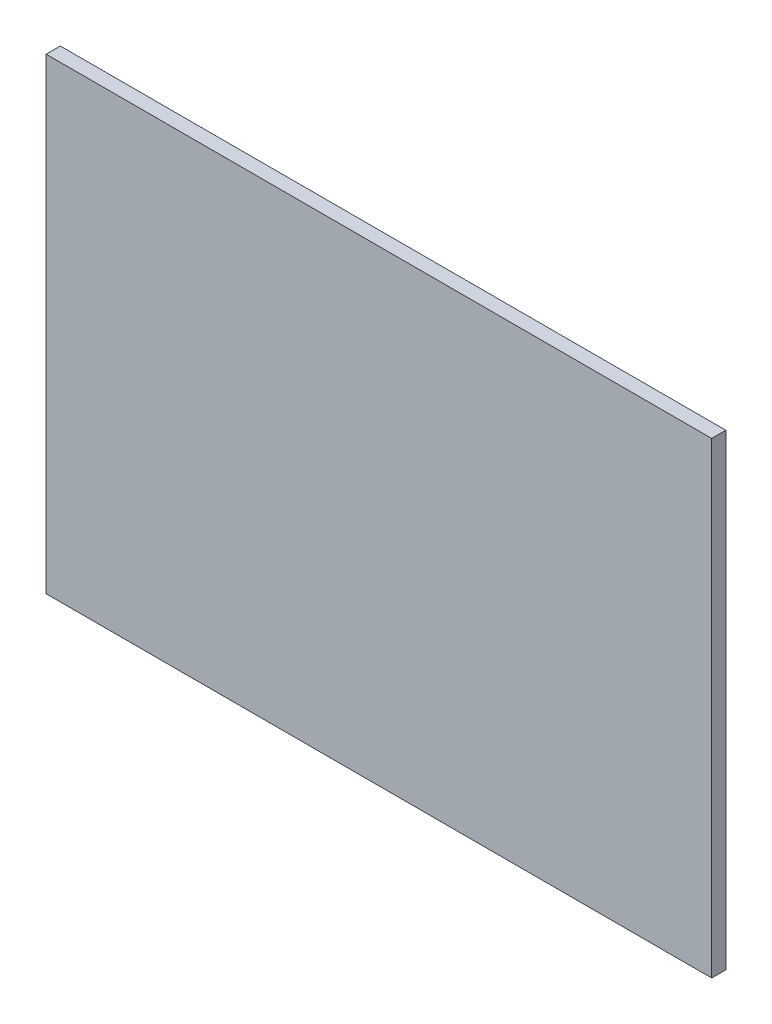
SolidWorks part; units mm, degrees
ref_plane "Спереди" through (0, 0, 0) normal (0, 0, 1) x (1, 0, 0)
ref_plane "Сверху" through (0, 0, 0) normal (0, 1, 0) x (1, 0, 0)
ref_plane "Справа" through (0, 0, 0) normal (1, 0, 0) x (0, 0, -1)
sketch "Эскиз1" plane through (0, 0, 0) normal (0, 0, 1) x (1, 0, 0)
  line L1 (0, 0) -> (470, 0)
  line L2 (0, 0) -> (0, 330)
  line L3 (0, 330) -> (470, 330)
  line L4 (470, 0) -> (470, 330)
extrude "Бобышка-Вытянуть1" add sketch "Эскиз1" along normal blind 10
